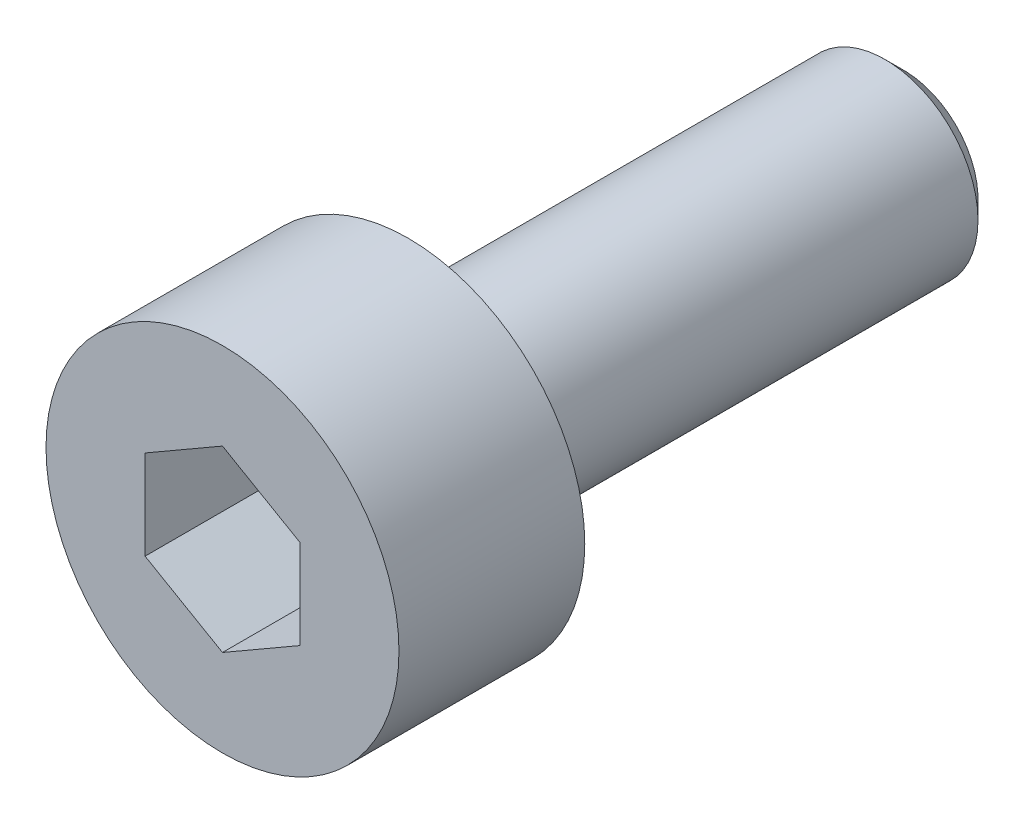
SolidWorks part; units mm, degrees
ref_plane "Front Plane" through (0, 0, 0) normal (0, 0, 1) x (1, 0, 0)
ref_plane "Top Plane" through (0, 0, 0) normal (0, 1, 0) x (1, 0, 0)
ref_plane "Right Plane" through (0, 0, 0) normal (1, 0, 0) x (0, 0, -1)
sketch "Sketch1" plane through (0, 0, 0) normal (0, 0, 1) x (1, 0, 0)
  circle A0 centre (0, 0) radius 2.85
  dimension "D1" = 5.7
extrude "Boss-Extrude1" add sketch "Sketch1" along normal blind 3
sketch "Sketch2" plane through (0, 0, 0) normal (0, 0, -1) x (-1, 0, 0)
  circle A0 centre (0, 0) radius 1.5
  dimension "D1" = 3
extrude "Boss-Extrude2" add sketch "Sketch2" along normal blind 8
chamfer "Chamfer1" distance 0.3 angle 45 1 edges at (-1.5, 0, -8)
sketch "Sketch3" plane through (0, 0, 3) normal (0, 0, 1) x (1, 0, 0)
  line L1 (0, 1.4434) -> (-1.25, 0.7217)
  line L2 (-1.25, 0.7217) -> (-1.25, -0.7217)
  line L3 (-1.25, -0.7217) -> (0, -1.4434)
  line L4 (0, -1.4434) -> (1.25, -0.7217)
  line L5 (1.25, -0.7217) -> (1.25, 0.7217)
  line L6 (1.25, 0.7217) -> (0, 1.4434)
  circle A0 centre (0, 0) radius 1.25 construction
  dimension "D1" = 2.5
extrude "Cut-Extrude1" cut sketch "Sketch3" against normal blind 2
